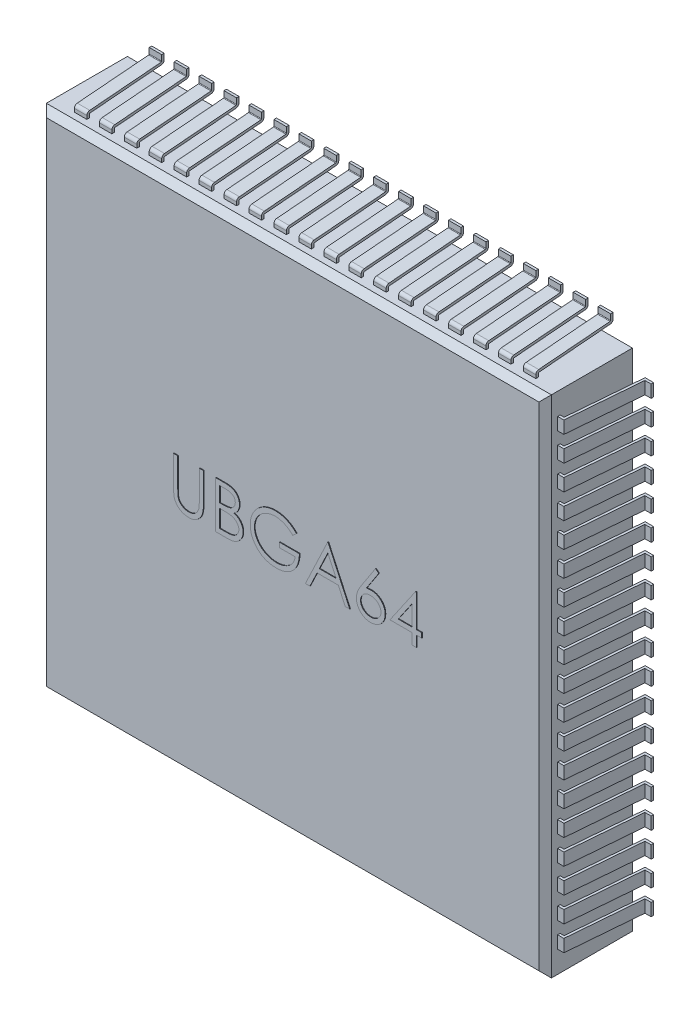
SolidWorks part; units mm, degrees
ref_plane "Front" through (0, 0, 0) normal (0, 0, 1) x (1, 0, 0)
ref_plane "Top" through (0, 0, 0) normal (0, 1, 0) x (1, 0, 0)
ref_plane "Right" through (0, 0, 0) normal (1, 0, 0) x (0, 0, -1)
sketch "COMPONENT_OUTLINE" plane through (0, 0, 0) normal (0, 0, 1) x (1, 0, 0)
  line L0 (-4.05, 4.05) -> (-4.05, -4.05)
  line L1 (-4.05, -4.05) -> (4.05, -4.05)
  line L2 (4.05, -4.05) -> (4.05, 4.05)
  line L3 (4.05, 4.05) -> (-4.05, 4.05)
extrude "Extrude1" add sketch "COMPONENT_OUTLINE" along normal blind 1.4
sketch "Sketch1" plane through (0, 0, 0) normal (1, 0, 0) x (0, 0, -1)
  line L0 (-1.2, 4.05) -> (-1.2, 4.15)
  line L1 (-1.4, 4.05) -> (0, 4.05) construction
  line L2 (-1.2, 4.15) -> (0, 4.25)
  line L3 (0, 4.25) -> (0, 4.35)
  dimension "D1" = 0.1
  dimension "D2" = 0.2
  dimension "D3" = 0.2
  dimension "D4" = 0.1
extrude "Extrude-Thin1" add sketch "Sketch1" along normal mid plane 0.2 thin
pattern_linear "LPattern1" count 10 spacing 0.4 along (-1, 0, 0) count 10 spacing 0.4 along (1, 0, 0) of "Extrude-Thin1"
mirror "Mirror1" about plane through (0, 0, 0) normal (0, 1, 0) of "Extrude-Thin1", "LPattern1"
sketch "Sketch2" plane through (0, 0, 0) normal (0, 1, 0) x (1, 0, 0)
  line L0 (4.05, -1.2) -> (4.15, -1.2)
  line L1 (4.05, -1.4) -> (4.05, 0) construction
  line L2 (4.15, -1.2) -> (4.25, 0)
  line L3 (4.25, 0) -> (4.35, 0)
  line L4 (4.05, -1.4) -> (-4.05, -1.4) construction
  dimension "D1" = 0.1
  dimension "D2" = 0.2
  dimension "D3" = 0.2
  dimension "D4" = 0.1
extrude "Extrude-Thin2" add sketch "Sketch2" along normal mid plane 0.2 thin thin type one direction reverse wall 0.04
pattern_linear "LPattern2" count 10 spacing 0.4 along (0, 1, 0) count 10 spacing 0.4 along (0, -1, 0) of "Extrude-Thin2"
mirror "Mirror2" about plane through (0, 0, 0) normal (1, 0, 0) of "LPattern2", "Extrude-Thin2"
chamfer "Chamfer1" distance 0.1 angle 45 4 edges at (4.05, 0, 1.4) (0, -4.05, 1.4) (-4.05, 0, 1.4) (0, 4.05, 1.4)
sketch "Sketch3" plane through (0, 0, 1.4) normal (0, 0, 1) x (1, 0, 0)
  text T0 "UBGA64" font "Century Gothic" height 0.75
extrude "Extrude2" add sketch "Sketch3" along normal blind 0.01
